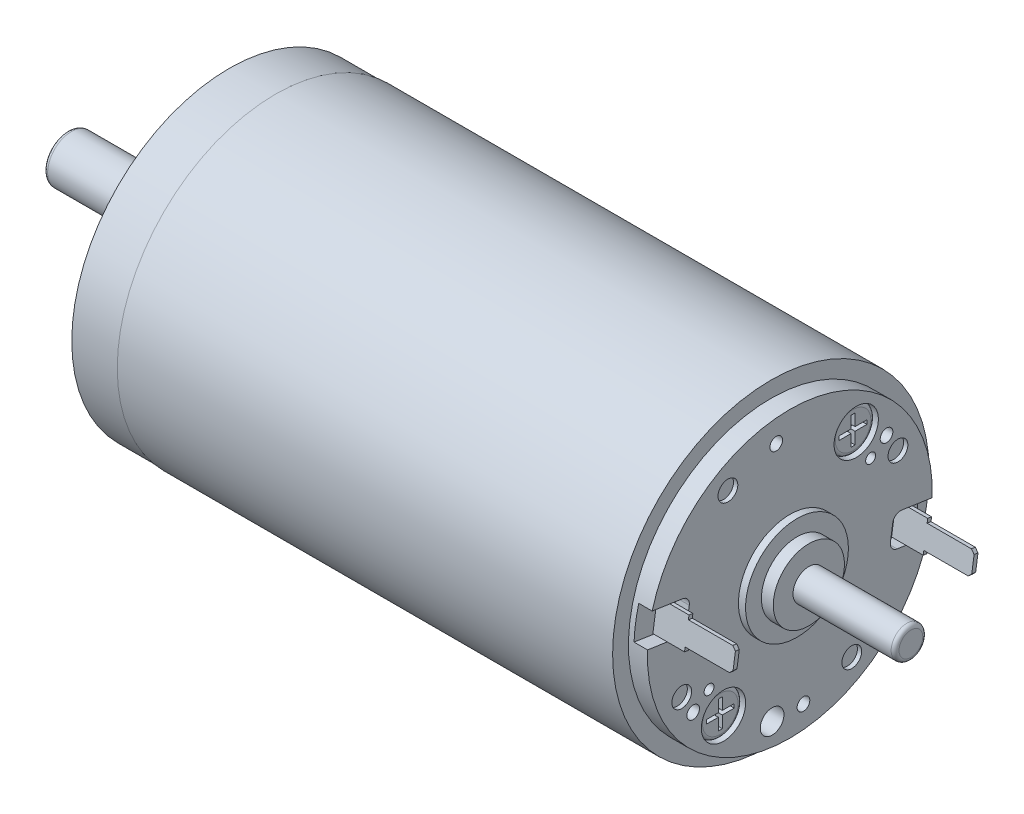
SolidWorks part; units mm, degrees
ref_plane "Ön Düzlem" through (0, 0, 0) normal (0, 0, 1) x (1, 0, 0)
ref_plane "Üst Düzlem" through (0, 0, 0) normal (0, 1, 0) x (1, 0, 0)
ref_plane "Sağ Düzlem" through (0, 0, 0) normal (1, 0, 0) x (0, 0, -1)
sketch "Çizim1" plane through (0, 0, 0) normal (0, 0, 1) x (1, 0, 0)
  line L0 (6, 20) -> (6, 0)
  line L1 (6, 0) -> (68.6, 0)
  line L2 (68.6, 0) -> (68.6, 20)
  line L3 (68.6, 20) -> (6, 20)
  line L4 (6, 0) -> (68.6, 0) construction
revolve "Döndür1" add sketch "Çizim1" angle 360 about L4
sketch "Çizim2" plane through (68.6, 0, 0) normal (1, 0, 0) x (0, 0, -1)
  circle A0 centre (0, 0) radius 18
extrude "Yükseklik-Ekstrüzyon1" add sketch "Çizim2" along normal blind 2.4
sketch "Çizim3" plane through (71, 0, 0) normal (1, 0, 0) x (0, 0, -1)
  line L0 (17.9877, -0.6661) -> (13.1528, 0.0565)
  line L1 (13.1528, 0.0565) -> (12.5616, -3.8996)
  line L2 (12.5616, -3.8996) -> (17.3964, -4.6221)
  arc A0 (17.3964, -4.6221) -> (17.9877, -0.6661) centre (0, 0) ccw
extrude "Kes-Ekstrüzyon1" cut sketch "Çizim3" against normal blind 1.7
sketch "Çizim4" plane through (69.3, 0, 0) normal (1, 0, 0) x (0, 0, -1)
  line L0 (15.0489, -4.1702) -> (14.5544, -4.0963)
  line L1 (14.5544, -4.0963) -> (15.1161, -0.338)
  line L2 (15.1161, -0.338) -> (15.6106, -0.4119)
  line L3 (15.6106, -0.4119) -> (15.0489, -4.1702)
extrude "Yükseklik-Ekstrüzyon2" add sketch "Çizim4" along normal blind 10
sketch "Çizim5" plane through (0, -2.2171, -14.8352) normal (0, 0.1478, 0.989) x (1, 0, 0)
  line L0 (73.3, 1.4) -> (79.3, 1.4)
  line L1 (79.3, 1.4) -> (79.3, 1.9)
  line L2 (79.3, 1.9) -> (73.3, 1.9)
  line L3 (73.3, 1.9) -> (73.3, 1.4)
extrude "Kes-Ekstrüzyon2" cut sketch "Çizim5" against normal through all
sketch "Çizim6" plane through (0, -2.2171, -14.8352) normal (0, 0.1478, 0.989) x (1, 0, 0)
  line L0 (73.3, -1.4) -> (73.3, -1.9)
  line L1 (73.3, -1.9) -> (79.3, -1.9)
  line L2 (79.3, -1.9) -> (79.3, -1.4)
  line L3 (79.3, -1.4) -> (73.3, -1.4)
extrude "Kes-Ekstrüzyon3" cut sketch "Çizim6" against normal through all
sketch "Çizim7" plane through (71, 0, 0) normal (1, 0, 0) x (0, 0, -1)
  line L0 (-17.9877, 0.6661) -> (-13.1528, -0.0565)
  line L1 (-13.1528, -0.0565) -> (-12.5616, 3.8996)
  line L2 (-12.5616, 3.8996) -> (-17.3964, 4.6221)
  arc A0 (-17.3964, 4.6221) -> (-17.9877, 0.6661) centre (0, 0) ccw
extrude "Kes-Ekstrüzyon4" cut sketch "Çizim7" against normal blind 1.7
sketch "Çizim8" plane through (69.3, 0, 0) normal (1, 0, 0) x (0, 0, -1)
  line L0 (-15.0489, 4.1702) -> (-14.5544, 4.0963)
  line L1 (-14.5544, 4.0963) -> (-15.1161, 0.338)
  line L2 (-15.1161, 0.338) -> (-15.6106, 0.4119)
  line L3 (-15.6106, 0.4119) -> (-15.0489, 4.1702)
extrude "Yükseklik-Ekstrüzyon3" add sketch "Çizim8" along normal blind 10
sketch "Çizim9" plane through (0, 2.2171, 14.8352) normal (0, -0.1478, -0.989) x (-1, 0, 0)
  line L0 (-79.3, -1.9) -> (-73.3, -1.9)
  line L1 (-73.3, -1.9) -> (-73.3, -1.4)
  line L2 (-73.3, -1.4) -> (-79.3, -1.4)
  line L3 (-79.3, -1.4) -> (-79.3, -1.9)
extrude "Kes-Ekstrüzyon5" cut sketch "Çizim9" against normal through all
sketch "Çizim10" plane through (0, 2.2171, 14.8352) normal (0, -0.1478, -0.989) x (-1, 0, 0)
  line L0 (-79.3, 1.9) -> (-79.3, 1.4)
  line L1 (-79.3, 1.4) -> (-73.3, 1.4)
  line L2 (-73.3, 1.4) -> (-73.3, 1.9)
  line L3 (-73.3, 1.9) -> (-79.3, 1.9)
extrude "Kes-Ekstrüzyon6" cut sketch "Çizim10" against normal through all
sketch "Çizim11" plane through (6, 0, 0) normal (-1, 0, 0) x (0, 0, 1)
  circle A0 centre (0, 0) radius 19.9
extrude "Yükseklik-Ekstrüzyon4" add sketch "Çizim11" along normal blind 5.85
sketch "Çizim12" plane through (0.15, 0, 0) normal (-1, 0, 0) x (0, 0, 1)
  circle A0 centre (0, 0) radius 18.5
extrude "Yükseklik-Ekstrüzyon5" add sketch "Çizim12" along normal blind 0.15
sketch "Çizim13" plane through (0, 0, 0) normal (-1, 0, 0) x (0, 0, 1)
  circle A0 centre (0, 0) radius 8
extrude "Yükseklik-Ekstrüzyon6" add sketch "Çizim13" along normal blind 1.4
sketch "Çizim14" plane through (-1.4, 0, 0) normal (-1, 0, 0) x (0, 0, 1)
  circle A0 centre (0, 0) radius 4.5
extrude "Yükseklik-Ekstrüzyon7" add sketch "Çizim14" along normal blind 2.15
sketch "Çizim15" plane through (-3.55, 0, 0) normal (-1, 0, 0) x (0, 0, 1)
  circle A0 centre (0, 0) radius 3
extrude "Yükseklik-Ekstrüzyon8" add sketch "Çizim15" along normal blind 16.75
sketch "Çizim16" plane through (71, 0, 0) normal (1, 0, 0) x (0, 0, -1)
  circle A0 centre (0, 0) radius 6.5
extrude "Yükseklik-Ekstrüzyon9" add sketch "Çizim16" along normal blind 0.9
sketch "Çizim17" plane through (71.9, 0, 0) normal (1, 0, 0) x (0, 0, -1)
  circle A0 centre (0, 0) radius 4.5
extrude "Yükseklik-Ekstrüzyon10" add sketch "Çizim17" along normal blind 1.5
sketch "Çizim18" plane through (73.4, 0, 0) normal (1, 0, 0) x (0, 0, -1)
  circle A0 centre (0, 0) radius 2
extrude "Yükseklik-Ekstrüzyon11" add sketch "Çizim18" along normal blind 12.9
hole_wizard "Ø5.6 (5.6) Çap Delik1" positions "Çizim20" profile "Çizim19" hole size "Ø5.6" standard "ANSI Metrik"
sketch "Çizim20" plane through (71, 0, 0) normal (1, 0, 0) x (0, 0, -1)
  point P0 (8.387, 11.3344)
sketch "Çizim19" plane through (71, 11.3344, -8.387) normal (0, 1, 0) x (0, 0, -1)
  line L0 (0, 0) -> (0, 2.4)
  line L1 (0, 2.4) -> (2.8, 2.4)
  line L2 (2.8, 2.4) -> (2.8, 0)
  line L5 (2.8, 0) -> (0, 0)
  line L10 (0, 2.4) -> (-2.8, 2.4) construction
  line L11 (0, -6.35) -> (0, 107.95) construction
  dimension "Hole Dia." = 5.6
  dimension "Hole Depth" = 2.4
  dimension "Drill Angle" = 180
sketch "Çizim21" plane through (68.6, 0, 0) normal (1, 0, 0) x (0, 0, -1)
  circle A0 centre (8.387, 11.3344) radius 2.75
extrude "Yükseklik-Ekstrüzyon12" add sketch "Çizim21" along normal blind 2
sketch "Çizim22" plane through (70.6, 0, 0) normal (1, 0, 0) x (0, 0, -1)
  line L0 (8.137, 13.0844) -> (8.137, 11.5844)
  line L1 (8.137, 11.5844) -> (6.637, 11.5844)
  line L2 (6.637, 11.5844) -> (6.637, 11.0844)
  line L3 (6.637, 11.0844) -> (8.137, 11.0844)
  line L4 (8.137, 11.0844) -> (8.137, 9.5844)
  line L5 (8.137, 9.5844) -> (8.637, 9.5844)
  line L6 (8.637, 9.5844) -> (8.637, 11.0844)
  line L7 (8.637, 11.0844) -> (10.137, 11.0844)
  line L8 (10.137, 11.0844) -> (10.137, 11.5844)
  line L9 (10.137, 11.5844) -> (8.637, 11.5844)
  line L10 (8.637, 11.5844) -> (8.637, 13.0844)
  line L11 (8.637, 13.0844) -> (8.137, 13.0844)
extrude "Kes-Ekstrüzyon7" cut sketch "Çizim22" against normal blind 0.86
hole_wizard "Ø5.6 (5.6) Çap Delik2" positions "Çizim24" profile "Çizim23" hole size "Ø5.6" standard "ANSI Metrik"
sketch "Çizim24" plane through (71, 0, 0) normal (1, 0, 0) x (0, 0, -1)
  point P0 (-8.387, -11.3344)
sketch "Çizim23" plane through (71, -11.3344, 8.387) normal (0, 1, 0) x (0, 0, -1)
  line L0 (0, 0) -> (0, 2.4)
  line L1 (0, 2.4) -> (2.8, 2.4)
  line L2 (2.8, 2.4) -> (2.8, 0)
  line L5 (2.8, 0) -> (0, 0)
  line L10 (0, 2.4) -> (-2.8, 2.4) construction
  line L11 (0, -6.35) -> (0, 107.95) construction
  dimension "Hole Dia." = 5.6
  dimension "Hole Depth" = 2.4
  dimension "Drill Angle" = 180
sketch "Çizim25" plane through (68.6, 0, 0) normal (1, 0, 0) x (0, 0, -1)
  circle A0 centre (-8.387, -11.3344) radius 2.75
extrude "Yükseklik-Ekstrüzyon13" add sketch "Çizim25" along normal blind 2
sketch "Çizim26" plane through (70.6, 0, 0) normal (1, 0, 0) x (0, 0, -1)
  line L0 (-8.637, -9.5844) -> (-8.637, -11.0844)
  line L1 (-8.637, -11.0844) -> (-10.137, -11.0844)
  line L2 (-10.137, -11.0844) -> (-10.137, -11.5844)
  line L3 (-10.137, -11.5844) -> (-8.637, -11.5844)
  line L4 (-8.637, -11.5844) -> (-8.637, -13.0844)
  line L5 (-8.637, -13.0844) -> (-8.137, -13.0844)
  line L6 (-8.137, -13.0844) -> (-8.137, -11.5844)
  line L7 (-8.137, -11.5844) -> (-6.637, -11.5844)
  line L8 (-6.637, -11.5844) -> (-6.637, -11.0844)
  line L9 (-6.637, -11.0844) -> (-8.137, -11.0844)
  line L10 (-8.137, -11.0844) -> (-8.137, -9.5844)
  line L11 (-8.137, -9.5844) -> (-8.637, -9.5844)
extrude "Kes-Ekstrüzyon8" cut sketch "Çizim26" against normal blind 0.86
hole_wizard "Ø3.0 (3) Çap Delik1" positions "Çizim28" profile "Çizim27" hole size "Ø3.0" standard "ANSI Metrik"
sketch "Çizim28" plane through (71, 0, 0) normal (1, 0, 0) x (0, 0, -1)
  point P0 (-2.243, -15.0348)
sketch "Çizim27" plane through (71, -15.0348, 2.243) normal (0, 1, 0) x (0, 0, -1)
  line L0 (0, 0) -> (0, 3.4)
  line L1 (0, 3.4) -> (1.5, 3.4)
  line L2 (1.5, 3.4) -> (1.5, 0)
  line L5 (1.5, 0) -> (0, 0)
  line L10 (0, 3.4) -> (-1.5, 3.4) construction
  line L11 (0, -6.35) -> (0, 107.95) construction
  dimension "Hole Dia." = 3
  dimension "Hole Depth" = 3.4
  dimension "Drill Angle" = 180
hole_wizard "Ø2.5 (2.5) Çap Delik1" positions "Çizim30" profile "Çizim29" hole size "Ø2.5" standard "ANSI Metrik"
sketch "Çizim30" plane through (71, 0, 0) normal (1, 0, 0) x (0, 0, -1)
  point P0 (7.8286, -13.0289)
  point P1 (-7.8286, 13.0289)
  point P2 (13.6617, 6.6632)
  point P3 (-13.6617, -6.6632)
sketch "Çizim29" plane through (71, -13.0289, -7.8286) normal (0, 1, 0) x (0, 0, -1)
  line L0 (0, 0) -> (0, 0.54)
  line L1 (0, 0.54) -> (1.25, 0.54)
  line L2 (1.25, 0.54) -> (1.25, 0)
  line L5 (1.25, 0) -> (0, 0)
  line L10 (0, 0.54) -> (-1.25, 0.54) construction
  line L11 (0, -6.35) -> (0, 107.95) construction
  dimension "Hole Dia." = 2.5
  dimension "Hole Depth" = 0.54
  dimension "Drill Angle" = 180
hole_wizard "Ø1.25 (1.25) Çap Delik1" positions "Çizim32" profile "Çizim31" hole size "Ø1.25" standard "ANSI Metrik"
sketch "Çizim32" plane through (71, 0, 0) normal (1, 0, 0) x (0, 0, -1)
  point P0 (10.209, 7.5542)
  point P1 (-10.209, -7.5542)
sketch "Çizim31" plane through (71, 7.5542, -10.209) normal (0, 1, 0) x (0, 0, -1)
  line L0 (0, 0) -> (0, 4.1108)
  line L1 (0, 4.1108) -> (0.625, 3.75)
  line L2 (0.625, 3.75) -> (0.625, 0)
  line L5 (0.625, 0) -> (0, 0)
  line L10 (0, 4.1108) -> (-0.625, 3.75) construction
  line L11 (0, -6.35) -> (0, 107.95) construction
  dimension "Hole Dia." = 1.25
  dimension "Hole Depth" = 3.75
  dimension "Drill Angle" = 120
hole_wizard "Ø1.6 (1.6) Çap Delik1" positions "Çizim34" profile "Çizim33" hole size "Ø1.6" standard "ANSI Metrik"
sketch "Çizim34" plane through (71, 0, 0) normal (1, 0, 0) x (0, 0, -1)
  point P0 (-1.7207, 15.1023)
  point P1 (1.7207, -15.1023)
  point P2 (12.2186, 9.0413)
  point P3 (-12.2186, -9.0413)
sketch "Çizim33" plane through (71, 15.1023, 1.7207) normal (0, 1, 0) x (0, 0, -1)
  line L0 (0, 0) -> (0, 5.2619)
  line L1 (0, 5.2619) -> (0.8, 4.8)
  line L2 (0.8, 4.8) -> (0.8, 0)
  line L5 (0.8, 0) -> (0, 0)
  line L10 (0, 5.2619) -> (-0.8, 4.8) construction
  line L11 (0, -6.35) -> (0, 107.95) construction
  dimension "Hole Dia." = 1.6
  dimension "Hole Depth" = 4.8
  dimension "Drill Angle" = 120
hole_wizard "Ø2.5 (2.5) Çap Delik2" positions "Çizim36" profile "Çizim35" hole size "Ø2.5" standard "ANSI Metrik"
sketch "Çizim36" plane through (0, 0, 0) normal (-1, 0, 0) x (0, 0, 1)
  point P0 (0, 11)
  point P1 (9.5263, 5.5)
  point P2 (9.5263, -5.5)
  point P3 (0, -11)
  point P4 (-9.5263, -5.5)
  point P5 (-9.5263, 5.5)
sketch "Çizim35" plane through (0, 11, 0) normal (0, 1, 0) x (0, 0, 1)
  line L0 (0, 0) -> (0, 8.2217)
  line L1 (0, 8.2217) -> (1.25, 7.5)
  line L2 (1.25, 7.5) -> (1.25, 0)
  line L5 (1.25, 0) -> (0, 0)
  line L10 (0, 8.2217) -> (-1.25, 7.5) construction
  line L11 (0, -6.35) -> (0, 107.95) construction
  dimension "Hole Dia." = 2.5
  dimension "Hole Depth" = 7.5
  dimension "Drill Angle" = 120
hole_wizard "Ø2.8 (2.8) Çap Delik1" positions "Çizim38" profile "Çizim37" hole size "Ø2.8" standard "ANSI Metrik"
sketch "Çizim38" plane through (0, 0, 0) normal (-1, 0, 0) x (0, 0, 1)
  point P0 (0, 15)
sketch "Çizim37" plane through (0, 15, 0) normal (0, 1, 0) x (0, 0, 1)
  line L0 (0, 0) -> (0, 2.0083)
  line L1 (0, 2.0083) -> (1.4, 1.2)
  line L2 (1.4, 1.2) -> (1.4, 0)
  line L5 (1.4, 0) -> (0, 0)
  line L10 (0, 2.0083) -> (-1.4, 1.2) construction
  line L11 (0, -6.35) -> (0, 107.95) construction
  dimension "Hole Dia." = 2.8
  dimension "Hole Depth" = 1.2
  dimension "Drill Angle" = 120
chamfer "Pah1" distance 0.4 angle 45 4 edges at (79.3, 3.6387, 14.8756) (79.3, 0.8695, 15.2894) (79.3, -0.8695, -15.2894) (79.3, -3.6387, -14.8756)
fillet "Radyus1" radius 0.5 4 edges at (-20.3, 0, 3) (70.6, 11.3344, -11.137) (70.6, -11.3344, 5.637) (86.3, 0, -2)
fillet "Radyus2" radius 1 4 edges at (70.15, -3.8996, -12.5616) (70.15, 3.8996, 12.5616) (70.15, 0.0565, -13.1528) (70.15, -0.0565, 13.1528)
